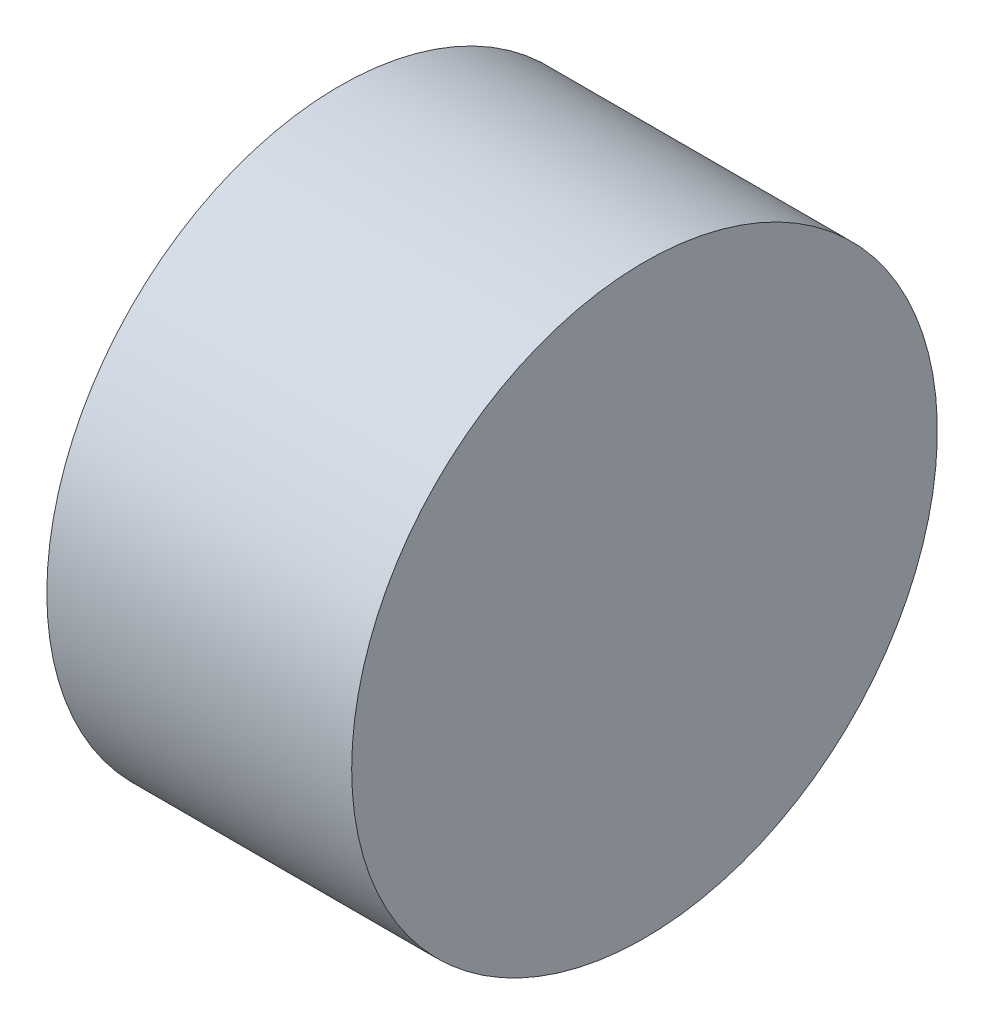
SolidWorks part; units mm, degrees
ref_plane "前视基准面" through (0, 0, 0) normal (0, 0, 1) x (1, 0, 0)
ref_plane "上视基准面" through (0, 0, 0) normal (0, 1, 0) x (1, 0, 0)
ref_plane "右视基准面" through (0, 0, 0) normal (1, 0, 0) x (0, 0, -1)
sketch "草图1" plane through (0, 0, 0) normal (0, 1, 0) x (1, 0, 0)
  line L0 (-159.6132, 0) -> (7821.0463, 0) construction
  line L1 (0, -159.6132) -> (0, 7821.0463) construction
  line L2 (0, 0) -> (-16.7, 0)
  line L3 (-16.7, 0) -> (-16.7, 3)
  line L4 (-16.7, 3) -> (-12.7, 3)
  line L5 (-12.7, 3) -> (-12.7, 12.2)
  line L6 (-12.7, 12.2) -> (0, 12.2)
  line L7 (0, 12.2) -> (0, 0)
  point P4 (-16.7, 0)
  dimension "D1" = 16.7
  dimension "D2" = 3
  dimension "D3" = 4
  dimension "D4" = 9.2
revolve "旋转1" add sketch "草图1" angle 360 about L0
sketch "草图3" plane through (-12.7, 0, 0) normal (-1, 0, 0) x (0, 0, 1)
  arc A0 (-8.668, 2.4219) -> (-8.8544, -1.6122) centre (0, 0) ccw
  arc A1 (-10.5942, 2.9601) -> (-10.8221, -1.9705) centre (0, 0) ccw
  arc A2 (-8.668, 2.4219) -> (-10.5942, 2.9601) centre (-9.9002, 1.7279) ccw
  arc A3 (-8.8544, -1.6122) -> (-10.8221, -1.9705) centre (-10.0174, -0.8075) cw
  arc A4 (6.4315, 6.2957) -> (3.031, 8.4743) centre (0, 0) ccw
  arc A5 (6.4315, 6.2957) -> (7.8607, 7.6948) centre (6.4465, 7.7099) ccw
  arc A6 (7.8607, 7.6948) -> (3.7045, 10.3574) centre (0, 0) ccw
  arc A7 (3.031, 8.4743) -> (3.7045, 10.3574) centre (4.3093, 9.0791) cw
  arc A8 (2.2365, -8.7177) -> (5.8234, -6.862) centre (0, 0) ccw
  arc A9 (2.2365, -8.7177) -> (2.7335, -10.6549) centre (3.4537, -9.4378) ccw
  arc A10 (2.7335, -10.6549) -> (7.1175, -8.3869) centre (0, 0) ccw
  arc A11 (5.8234, -6.862) -> (7.1175, -8.3869) centre (5.708, -8.2715) cw
  circle A12 centre (0, 0) radius 3 construction
  point P11 (-10.5942, 2.9601)
  point P12 (-10.8221, -1.9705)
  point P13 (-8.8544, -1.6122)
  point P14 (-8.668, 2.4219)
  point P27 (0, 0)
  dimension "D1" = 18
  dimension "D2" = 22
  dimension "D3" = 1.4142
  dimension "D5" = 1.4142
  dimension "D6" = 2.2365
  dimension "D7" = 2.7335
  dimension "D8" = 3.031
  dimension "D9" = 3.7045
  dimension "D4" = 3
extrude "切除-拉伸1" cut sketch "草图3" against normal blind 3
sketch "草图4" plane through (-12.7, 0, 0) normal (-1, 0, 0) x (0, 0, 1)
  line L0 (-8.668, 2.4219) -> (3.031, 8.4743) construction
  line L1 (0, 0) -> (-22974.5091, 44409.1424) construction
  point P3 (-8.668, 2.4219)
  point P4 (3.031, 8.4743)
  point P9 (-2.8185, 5.4481)
  point P12 (-4.1354, 7.9936)
  point P27 (-11487.2546, 22204.5712)
  circle B0 centre (-2.8185, 5.4481) radius 0.75
  circle B1 centre (-4.1354, 7.9936) radius 0.75
  circle B2 centre (8.9904, -0.4155) radius 0.75
  circle B3 centre (6.1274, -0.2832) radius 0.75
  circle B4 centre (-4.855, -7.5782) radius 0.75
  circle B5 centre (-3.3089, -5.1649) radius 0.75
  dimension "D1" = 11493.686
sketch_block_instance "块1-1"
sketch_block "块1" parameters "D1"=1.5, "D2"=1.5
extrude "切除-拉伸2" cut sketch "草图4" against normal blind 3
sketch "草图6" plane through (-12.7, 0, 0) normal (-1, 0, 0) x (0, 0, 1)
  line L0 (0, -49000) -> (0, 49000) construction
  point P1 (0, 5.0835)
  point P4 (0, -5.0835)
  point P7 (0, 0)
  circle B0 centre (0, 5.0835) radius 0.65
  circle B1 centre (0, -5.0835) radius 0.65
  dimension "D2" = 5.2739
  dimension "D1" = 2
sketch_block_instance "块2-1"
sketch_block "块2" parameters "D1"=1.3, "D2"=1.3
extrude "切除-拉伸3" cut sketch "草图6" against normal blind 3
